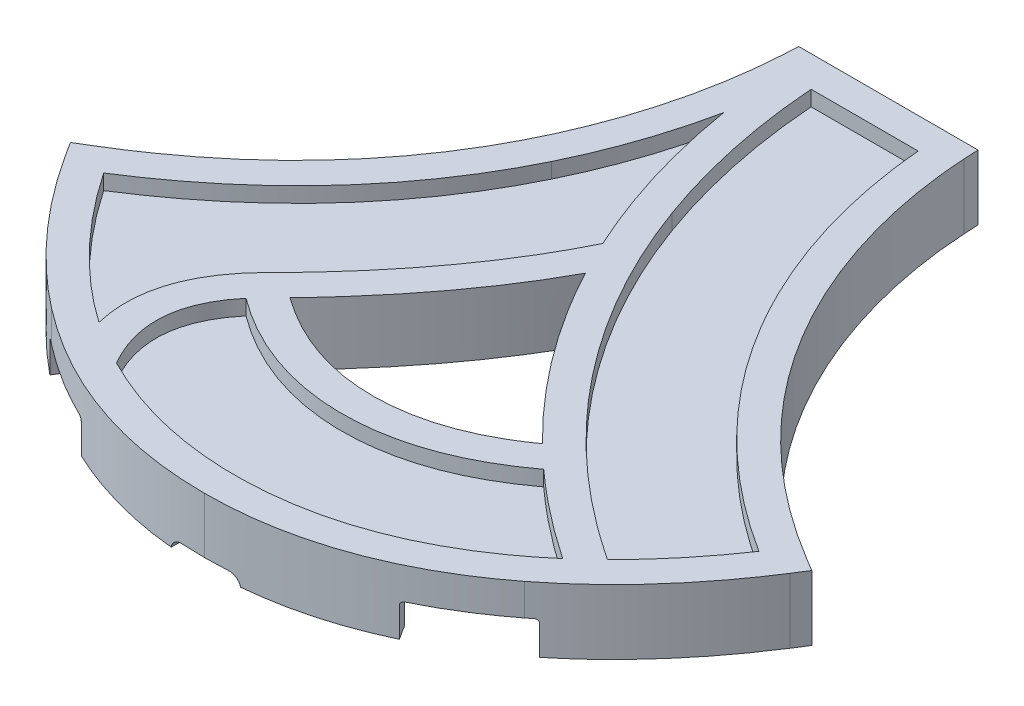
SolidWorks part; units mm, degrees
material "Default Heavy"
ref_plane "Front \"XY\"" through (0, 0, 0) normal (0, 0, 1) x (1, 0, 0)
ref_plane "Top \"XZ\"" through (0, 0, 0) normal (0, 1, 0) x (1, 0, 0)
ref_plane "Right \"YZ\"" through (0, 0, 0) normal (1, 0, 0) x (0, 0, -1)
sketch "Sketch1" plane through (0, 0, 0) normal (0, 1, 0) x (1, 0, 0)
  line L32 (11.7402, 44.8006) -> (-11.7315, 44.8006) construction
  line L33 (11.7402, 44.8006) -> (-11.7315, 44.8006) construction
  line L34 (-46.7664, -12.7009) -> (-48.5396, -13.7694) construction
  line L35 (-11.7315, 44.8006) -> (-11.8354, 42.8927) construction
  line L36 (47.433, -15.5188) -> (48.547, -13.7736) construction
  line L37 (-48.5396, -13.7694) -> (-47.426, -15.5143) construction
  line L38 (11.8441, 42.8927) -> (11.7402, 44.8006) construction
  line L39 (48.547, -13.7736) -> (46.7735, -12.7051) construction
  line L40 (11.7402, 44.8006) -> (-11.7315, 44.8006)
  line L41 (11.7402, 44.8006) -> (-11.7315, 44.8006)
  line L42 (-46.7664, -12.7009) -> (-48.5396, -13.7694)
  line L43 (-11.7315, 44.8006) -> (-11.8354, 42.8927)
  line L44 (47.433, -15.5188) -> (48.547, -13.7736)
  line L45 (-48.5396, -13.7694) -> (-47.426, -15.5143)
  line L46 (11.8441, 42.8927) -> (11.7402, 44.8006)
  line L47 (48.547, -13.7736) -> (46.7735, -12.7051)
  line L48 (11.7402, 44.8006) -> (-11.7315, 44.8006)
  spline S16 degree 3 poles (13707.5926, -20824.3124) (-15245.721, 20050.3834) (16897.5102, -18500.0295) (-18773.6133, 16415.021) knots -4.837537 -4.837537 -4.837537 -4.837537 13.412355 13.412355 13.412355 13.412355 only from (-11.8354, 42.8927) to (-46.7664, -12.7009) construction
  spline S17 degree 3 poles (1539.6845, -24946.8696) (-345.1015, 25306.6263) (-1470.73, -25271.221) (3595.9316, 24629.0284) knots -11.779696 -11.779696 -11.779696 -11.779696 27.004218 27.004218 27.004218 27.004218 only from (-47.426, -15.5143) to (-30.9593, -33.8177) construction
  spline S18 degree 3 poles (21323.4082, 11255.2499) (-19481.8243, 1044.4638) (16093.481, -12042.5003) (-11459.5819, 21515.9032) knots -31.449224 -31.449224 -31.449224 -31.449224 46.962215 46.962215 46.962215 46.962215 only from (-30.9593, -33.8177) to (0.0044, -44.7764) construction
  spline S19 degree 3 poles (11483.557, 21502.7967) (-16112.02, -12023.9333) (19492.4249, 1026.6895) (-21324.7799, 11264.6859) knots -28.966744 -28.966744 -28.966744 -28.966744 49.442095 49.442095 49.442095 49.442095 only from (0.0044, -44.7764) to (30.9639, -33.8206) construction
  spline S21 degree 3 poles (-3597.2153, 24627.9956) (1471.8367, -25270.9645) (344.2614, 25307.2023) (-1539.1086, -24948.3129) knots -9.003943 -9.003943 -9.003943 -9.003943 29.780059 29.780059 29.780059 29.780059 only from (30.9639, -33.8206) to (47.433, -15.5188) construction
  spline S23 degree 3 poles (18768.5213, 16420.8604) (-16891.8994, -18504.907) (15239.7814, 20054.0475) (-13701.4196, -20826.6216) knots -8.411838 -8.411838 -8.411838 -8.411838 9.836602 9.836602 9.836602 9.836602 only from (46.7735, -12.7051) to (11.8441, 42.8927) construction
  spline S27 degree 3 poles (-11.8354, 42.8927) (-12.42, 32.1531) (-16.9942, 5.2374) (-46.7664, -12.7009) knots 4 4 4 4 5 5 5 5
  spline S28 degree 3 poles (-47.426, -15.5143) (-44.2218, -20.5355) (-38.764, -27.7869) (-30.9593, -33.8177) knots 7 7 7 7 8 8 8 8
  spline S29 degree 3 poles (-30.9593, -33.8177) (-21.5489, -41.0893) (-11.1312, -44.7764) (0.0044, -44.7764) knots 8 8 8 8 9 9 9 9
  spline S30 degree 3 poles (0.0044, -44.7764) (11.1376, -44.7764) (21.554, -41.0903) (30.9639, -33.8206) knots 9 9 9 9 10 10 10 10
  spline S31 degree 3 poles (30.9639, -33.8206) (38.7697, -27.7903) (44.2283, -20.5394) (47.433, -15.5188) knots 10 10 10 10 11 11 11 11
  spline S32 degree 3 poles (46.7735, -12.7051) (17.0035, 5.2298) (12.4291, 32.1508) (11.8441, 42.8927) knots 0 0 0 0 1 1 1 1
  spline S33 degree 3 poles (-22689.4131, 7516.3472) (50.058, 6093.499) (323.9531, -22.7171) (0.0044, -22.7171) (-324.142, -22.7171) (-49.4306, 6101.5423) (22711.8041, 7432.6911) knots -55.485032 -55.485032 -55.485032 -55.485032 1 1 1 57.365232 57.365232 57.365232 57.365232 only from (16.5263, -17.0261) to (-16.5604, -16.995) construction
  spline S34 degree 3 poles (-11026.4564, -22396.6328) (12800.7603, 21635.8317) (-14894.9391, -20098.3724) (17282.0639, 17882.0255) knots -25.324219 -25.324219 -25.324219 -25.324219 30.628889 30.628889 30.628889 30.628889 only from (0, 5.1275) to (16.5263, -17.0261) construction
  spline S35 degree 3 poles (1892.6976, 23618.6805) (-11466.4056, -21362.8263) (17398.9855, 17827.8021) (-20670.1303, -13617.4284) knots -53.46671 -53.46671 -53.46671 -53.46671 51.151619 51.151619 51.151619 51.151619 only from (-16.5604, -16.995) to (0, 5.1275) construction
  spline S36 degree 3 poles (16.5263, -17.0261) (11.2873, -20.8001) (5.7395, -22.7171) (0.0044, -22.7171) (-5.7464, -22.7171) (-11.3088, -20.7894) (-16.5604, -16.995) knots 0 0 0 0 1 1 1 2 2 2 2
  spline S37 degree 3 poles (0, 5.1275) (3.7422, -1.9338) (9.039, -9.6332) (16.5263, -17.0261) knots 3 3 3 3 4 4 4 4
  spline S38 degree 3 poles (-16.5604, -16.995) (-9.5786, -9.7673) (-4.0267, -2.348) (0, 5.1275) knots 2 2 2 2 3 3 3 3
extrude "Boss-Extrude1" add sketch "Sketch1" along normal blind 2.5 contours L47 S32 L46 L40 L43 S27 L42 L45 S28 S29 S30 S31 L44 S36 S38 S37
sketch "Sketch4" plane through (0, 0, 0) normal (0, -1, 0) x (1, 0, 0)
  line L10 (11.8441, -42.8927) -> (11.7402, -44.8006) construction
  line L11 (48.547, 13.7736) -> (46.7735, 12.7051) construction
  line L12 (11.7402, -44.8006) -> (-11.7315, -44.8006) construction
  line L13 (-46.7664, 12.7009) -> (-48.5396, 13.7694) construction
  line L14 (-11.7315, -44.8006) -> (-11.8354, -42.8927) construction
  line L15 (47.433, 15.5188) -> (48.547, 13.7736) construction
  line L16 (-48.5396, 13.7694) -> (-47.426, 15.5143) construction
  line L17 (11.8441, -42.8927) -> (11.7402, -44.8006)
  line L18 (48.547, 13.7736) -> (46.7735, 12.7051)
  line L19 (11.7402, -44.8006) -> (-11.7315, -44.8006)
  line L20 (-46.7664, 12.7009) -> (-48.5396, 13.7694)
  line L21 (-11.7315, -44.8006) -> (-11.8354, -42.8927)
  line L22 (47.433, 15.5188) -> (48.547, 13.7736)
  line L23 (-48.5396, 13.7694) -> (-47.426, 15.5143)
  line L27 (7.0684, -42.5506) -> (-7.0596, -42.5506)
  line L31 (-45.4008, 14.5046) -> (-45.4008, 14.5046) construction
  line L32 (-45.4008, 14.5046) -> (-45.4008, 14.5046) construction
  line L33 (45.4079, 14.5088) -> (45.4079, 14.5088) construction
  line L34 (45.4079, 14.5088) -> (45.4079, 14.5088) construction
  line L35 (9.6098, -42.5506) -> (-9.6011, -42.5506) construction
  line L36 (-9.6011, -42.5506) -> (-9.6011, -42.5506) construction
  line L37 (9.6098, -42.5506) -> (9.6098, -42.5506) construction
  arc A8 (-43.7947, 16.9011) -> (-43.039, 13.0216) centre (-41.5398, 15.327) ccw
  arc A9 (43.8013, 16.9056) -> (43.0458, 13.0258) centre (41.5466, 15.3312) cw
  arc A10 (-9.7963, -40.0708) -> (-7.0596, -42.5506) centre (-7.0596, -39.8006) ccw
  arc A11 (7.0684, -42.5506) -> (9.8051, -40.0708) centre (7.0684, -39.8006) ccw
  arc A12 (-18.5794, 18.3121) -> (-18.7798, 16.0541) centre (-17.7009, 17.0963) ccw
  arc A13 (18.5615, 18.3331) -> (18.7386, 16.0486) centre (17.6847, 17.116) cw
  arc A14 (-1.3152, -7.4304) -> (1.3308, -7.4214) centre (0.0054, -6.719) ccw
  spline S0 degree 1 poles (-45.4008, 14.5046) (-29.5836, 32.0373) knots 0 0 1 1 construction
  spline S1 degree 1 poles (-29.5836, 32.0373) (0.0044, 42.5264) knots 0 0 1 1 construction
  spline S2 degree 1 poles (0.0044, 42.5264) (29.5883, 32.04) knots 0 0 1 1 construction
  spline S3 degree 1 poles (29.5883, 32.04) (45.4079, 14.5088) knots 0 0 1 1 construction
  spline S4 degree 1 poles (45.4079, 14.5088) (9.6098, -42.5506) knots 0 0 1 1 construction
  spline S5 degree 1 poles (-9.6011, -42.5506) (-45.4008, 14.5046) knots 0 0 1 1 construction
  spline S6 degree 3 poles (1803.2949, -917.1286) (-1413.7247, 1426.3175) (1143.7595, -1785.5106) (-885.202, 1742.7475) knots -3.201509 -3.201509 -3.201509 -3.201509 4.674641 4.674641 4.674641 4.674641 only from (46.7735, 12.7051) to (11.8441, -42.8927) construction
  spline S7 degree 3 poles (885.5961, 1742.5426) (-1144.1453, -1785.128) (1414.1117, 1425.791) (-1803.61, -916.5575) knots 0.325017 0.325017 0.325017 0.325017 8.201625 8.201625 8.201625 8.201625 only from (-11.8354, -42.8927) to (-46.7664, 12.7009) construction
  spline S8 degree 3 poles (-656.5291, -1830.5216) (211.0906, 2136.1853) (197.0374, -2121.6865) (-250.135, 1992.3469) knots 1.9887 1.9887 1.9887 1.9887 18.868565 18.868565 18.868565 18.868565 only from (30.9639, 33.8206) to (47.433, 15.5188) construction
  spline S9 degree 3 poles (-182.7302, -1916.5345) (-625.9753, 964.0535) (972.7294, 379.8096) (-706.3522, -1787.4548) knots -3.602256 -3.602256 -3.602256 -3.602256 22.781955 22.781955 22.781955 22.781955 only from (0.0044, 44.7764) to (30.9639, 33.8206) construction
  spline S10 degree 3 poles (706.2836, -1787.507) (-972.1545, 379.053) (624.8527, 964.7445) (184.0184, -1916.4925) knots -4.782528 -4.782528 -4.782528 -4.782528 21.598996 21.598996 21.598996 21.598996 only from (-30.9593, 33.8177) to (0.0044, 44.7764) construction
  spline S11 degree 3 poles (250.1669, 1992.3048) (-197.0811, -2121.6951) (-210.9874, 2136.2153) (656.3732, -1830.5639) knots -0.86853 -0.86853 -0.86853 -0.86853 16.011373 16.011373 16.011373 16.011373 only from (-47.426, 15.5143) to (-30.9593, 33.8177) construction
  spline S12 degree 3 poles (46.7735, 12.7051) (17.0035, -5.2298) (12.4291, -32.1508) (11.8441, -42.8927) knots 0 0 0 0 1 1 1 1
  spline S13 degree 3 poles (-11.8354, -42.8927) (-12.42, -32.1531) (-16.9942, -5.2374) (-46.7664, 12.7009) knots 4 4 4 4 5 5 5 5
  spline S14 degree 1 poles (20.0016, 17.2956) (-19.982, 17.2987) knots 0 0 1 1 construction
  spline S15 degree 1 poles (-19.982, 17.2987) (0.0161, -9.902) knots 0 0 1 1 construction
  spline S16 degree 1 poles (0.0161, -9.902) (20.0016, 17.2956) knots 0 0 1 1 construction
  spline S17 degree 3 poles (-656.972, 1882.3837) (895.1742, -1896.2916) (-1266.5252, 1551.0515) (1736.0801, -964.3246) knots -9.517328 -9.517328 -9.517328 -9.517328 14.561888 14.561888 14.561888 14.561888 only from (0, -5.1275) to (16.5263, 17.0261) construction
  spline S18 degree 3 poles (-812.1216, -1756.1775) (153.3939, -723.9366) (113.1908, 22.7171) (0.0044, 22.7171) (-113.2755, 22.7171) (-153.4167, -725.2403) (813.7688, -1755.1904) knots -18.735656 -18.735656 -18.735656 -18.735656 1 1 1 20.698036 20.698036 20.698036 20.698036 only from (16.5263, 17.0261) to (-16.5604, 16.995) construction
  spline S19 degree 3 poles (-1494.9401, -1107.0542) (-493.0371, 1462.3088) (1527.6763, -1118.2051) (-1935.6902, 373.726) knots -19.400052 -19.400052 -19.400052 -19.400052 21.459168 21.459168 21.459168 21.459168 only from (-16.5604, 16.995) to (0, -5.1275) construction
  spline S20 degree 3 poles (30.9639, 33.8206) (38.7697, 27.7903) (44.2283, 20.5394) (47.433, 15.5188) knots 10 10 10 10 11 11 11 11
  spline S21 degree 3 poles (0.0044, 44.7764) (11.1376, 44.7764) (21.554, 41.0903) (30.9639, 33.8206) knots 9 9 9 9 10 10 10 10
  spline S22 degree 3 poles (-30.9593, 33.8177) (-21.5489, 41.0893) (-11.1312, 44.7764) (0.0044, 44.7764) knots 8 8 8 8 9 9 9 9
  spline S23 degree 3 poles (-47.426, 15.5143) (-44.2218, 20.5355) (-38.764, 27.7869) (-30.9593, 33.8177) knots 7 7 7 7 8 8 8 8
  spline S24 degree 3 poles (-45.4008, 14.5046) (-45.1993, 14.818) (-44.8052, 15.4216) (-44.3123, 16.1525) (-43.9137, 16.7311) (-43.4344, 17.4177) (-42.4848, 18.7375) (-41.0114, 20.6683) (-38.5096, 23.7002) (-35.6003, 26.8157) (-32.3026, 29.8474) (-30.4978, 31.3308) (-29.5836, 32.0373) knots 7.013641 7.013641 7.013641 7.013641 7.075288 7.135505 7.150917 7.181741 7.260231 7.383525 7.50682 7.75341 7.876705 8 8 8 8 only from (-43.7947, 16.9011) to (-29.5836, 32.0373)
  spline S25 degree 3 poles (-29.5836, 32.0373) (-29.0215, 32.4716) (-27.875, 33.3247) (-25.5723, 34.9076) (-22.6403, 36.6839) (-19.0496, 38.4843) (-14.1648, 40.4483) (-9.1321, 41.7588) (-3.9659, 42.4164) (-1.3145, 42.5264) (0.0044, 42.5264) knots 8 8 8 8 8.0625 8.125 8.25 8.375 8.5 8.75 8.875 9 9 9 9
  spline S26 degree 3 poles (0.0044, 42.5264) (1.323, 42.5264) (3.9739, 42.4164) (9.1391, 41.759) (14.171, 40.4488) (19.0553, 38.4854) (22.6455, 36.6855) (25.5773, 34.9097) (27.8799, 33.3271) (29.0263, 32.4742) (29.5883, 32.04) knots 9 9 9 9 9.125 9.25 9.5 9.625 9.75 9.875 9.9375 10 10 10 10
  spline S27 degree 3 poles (29.5883, 32.04) (30.5027, 31.3336) (32.3078, 29.8503) (35.6059, 26.8189) (38.5156, 23.7036) (41.0179, 20.672) (42.4913, 18.7415) (43.441, 17.422) (43.9203, 16.7355) (44.3191, 16.1569) (44.8122, 15.4259) (45.2064, 14.8222) (45.4079, 14.5088) knots 9.999999 9.999999 9.999999 9.999999 10.123294 10.246588 10.493177 10.616472 10.739766 10.81823 10.849054 10.864466 10.924708 10.986355 10.986355 10.986355 10.986355 only from (29.5883, 32.04) to (43.8013, 16.9056)
  spline S28 degree 3 poles (45.4079, 14.5088) (44.8128, 14.1482) (43.8135, 13.5262) (42.0129, 12.3551) (39.0954, 10.3496) (35.1379, 7.2909) (30.8576, 3.4304) (25.8129, -1.8595) (20.6827, -8.6402) (16.1679, -16.7402) (13.048, -24.4997) (11.4011, -30.4358) (10.5296, -34.7203) (10.098, -37.4733) (9.8808, -39.3004) (9.7577, -40.5487) (9.6768, -41.5052) (9.6313, -42.1823) (9.6098, -42.5506) knots 0.002236 0.002236 0.002236 0.002236 0.022081 0.035311 0.064191 0.126145 0.1881 0.250054 0.373963 0.497872 0.621781 0.74569 0.807644 0.869598 0.919268 0.934756 0.96253 0.993507 0.993507 0.993507 0.993507 only from (43.0458, 13.0258) to (9.8051, -40.0708)
  spline S29 degree 3 poles (-9.6011, -42.5506) (-9.6225, -42.1824) (-9.668, -41.5053) (-9.7489, -40.5488) (-9.872, -39.3007) (-10.0891, -37.4741) (-10.5207, -34.7218) (-11.3922, -30.438) (-13.0391, -24.5029) (-16.1591, -16.7443) (-20.6741, -8.6451) (-25.8046, -1.8647) (-30.8496, 3.4252) (-35.1301, 7.2858) (-39.0881, 10.3449) (-42.0059, 12.3507) (-43.8066, 13.522) (-44.8058, 14.1439) (-45.4008, 14.5046) knots 4.006495 4.006495 4.006495 4.006495 4.037472 4.065257 4.080746 4.130403 4.192358 4.254312 4.378221 4.502129 4.626038 4.749947 4.811901 4.873855 4.93581 4.964697 4.977924 4.997764 4.997764 4.997764 4.997764 only from (-9.7963, -40.0708) to (-43.039, 13.0216)
  spline S30 degree 3 poles (0, -5.1275) (3.7422, 1.9338) (9.039, 9.6332) (16.5263, 17.0261) knots 3 3 3 3 4 4 4 4
  spline S31 degree 3 poles (16.5263, 17.0261) (11.2873, 20.8001) (5.7395, 22.7171) (0.0044, 22.7171) (-5.7464, 22.7171) (-11.3088, 20.7894) (-16.5604, 16.995) knots 0 0 0 0 1 1 1 2 2 2 2
  spline S32 degree 3 poles (-16.5604, 16.995) (-9.5786, 9.7673) (-4.0267, 2.348) (0, -5.1275) knots 2 2 2 2 3 3 3 3
  spline S33 degree 3 poles (20.0016, 17.2956) (19.6138, 17.575) (19.0409, 17.9876) (18.2984, 18.5226) (17.5637, 19.0513) (16.5747, 19.7393) (14.9744, 20.7501) (12.9322, 21.8797) (9.603, 23.366) (5.3275, 24.6235) (0.0454, 25.1357) (-5.2638, 24.6357) (-9.5496, 23.3824) (-12.8892, 21.8968) (-14.9374, 20.7667) (-16.5425, 19.7545) (-17.5489, 19.0561) (-18.3022, 18.5124) (-19.0462, 17.9748) (-19.6063, 17.5701) (-19.982, 17.2987) knots -0.137443 -0.137443 -0.137443 -0.137443 -0.063557 -0.028072 0.004493 0.075461 0.14643 0.288366 0.430303 0.714176 0.998049 1.281922 1.565795 1.707732 1.849668 1.920636 1.991605 2.026772 2.062256 2.133541 2.133541 2.133541 2.133541 only from (18.5615, 18.3331) to (-18.5794, 18.3121)
  spline S34 degree 3 poles (-19.982, 17.2987) (-19.6814, 16.9876) (-19.1812, 16.4694) (-18.5789, 15.8463) (-17.7934, 15.0311) (-16.1628, 13.3221) (-13.6979, 10.5792) (-10.8922, 7.2085) (-7.4378, 2.6925) (-4.7989, -1.2759) (-2.8048, -4.685) (-2.0802, -6.0114) (-1.5014, -7.0846) (-0.8713, -8.2547) (-0.3489, -9.2243) (0.0161, -9.902) knots 1.913903 1.913903 1.913903 1.913903 1.956951 1.98565 2 2.070329 2.226756 2.383183 2.539609 2.852463 2.930676 3.00889 3.035552 3.074659 3.165316 3.165316 3.165316 3.165316 only from (-18.7798, 16.0541) to (-1.3152, -7.4304)
  spline S35 degree 3 poles (0.0161, -9.902) (0.3448, -9.2819) (0.8926, -8.2494) (1.5498, -7.0071) (2.4005, -5.4132) (4.2333, -2.0674) (7.0594, 2.3493) (10.4823, 6.9426) (13.335, 10.3966) (15.9235, 13.233) (17.6722, 14.9929) (18.5275, 15.8403) (19.1605, 16.4648) (19.6859, 16.9839) (20.0016, 17.2956) knots 2.824352 2.824352 2.824352 2.824352 2.912176 2.970725 3 3.139349 3.454347 3.611845 3.769344 3.926842 4 4.014057 4.042171 4.084341 4.084341 4.084341 4.084341 only from (1.3308, -7.4214) to (18.7386, 16.0486)
  dimension "D3" = 2.25
  dimension "D2" = 2.75
  dimension "D4" = 1.5
  dimension "D1" = 2.25
extrude "Boss-Extrude4" add sketch "Sketch4" along normal blind 4
sketch "Sketch15" plane through (0, 0, 0) normal (0, -1, 0) x (1, 0, 0)
  arc A12 (39.5784, 17.9174) -> (38.8845, 13.4669) centre (41.5466, 15.3312) ccw
  arc A13 (43.0458, 13.0258) -> (43.8013, 16.9056) centre (41.5466, 15.3312) ccw construction
  arc A14 (38.2872, 9.6934) -> (38.8845, 13.4669) centre (36.6319, 11.8894) ccw
  arc A15 (39.5784, 17.9174) -> (40.0305, 21.8605) centre (37.913, 20.1058) ccw
  arc A16 (43.0458, 13.0258) -> (43.8013, 16.9056) centre (41.5466, 15.3312) ccw construction
  arc A17 (43.0458, 13.0258) -> (43.8013, 16.9056) centre (41.5466, 15.3312) ccw
  arc A18 (-39.5719, 17.9135) -> (-38.8777, 13.4627) centre (-41.5398, 15.327) cw
  arc A19 (-38.8777, 13.4627) -> (-38.2805, 9.6891) centre (-36.6252, 11.8851) ccw
  arc A20 (-39.5719, 17.9135) -> (-40.0245, 21.8565) centre (-37.9068, 20.1021) cw
  arc A21 (-43.7947, 16.9011) -> (-43.039, 13.0216) centre (-41.5398, 15.327) ccw construction
  arc A22 (-43.7947, 16.9011) -> (-43.039, 13.0216) centre (-41.5398, 15.327) ccw
  arc A23 (-2.7443, -9.6779) -> (2.7511, -9.6688) centre (0.0054, -10.8775) ccw
  arc A26 (-1.3152, -7.4304) -> (1.3308, -7.4214) centre (0.0054, -6.719) ccw construction
  arc A32 (2.2258, -8.8602) -> (-2.218, -8.8634) centre (0.0054, -10.8775) ccw construction
  arc A33 (2.7511, -9.6688) -> (3.0034, -4.3271) centre (8.2425, -7.2513) cw
  arc A34 (-2.7443, -9.6779) -> (-3.0409, -4.2901) centre (-8.2437, -7.2786) ccw
  arc A35 (-1.3152, -7.4304) -> (1.3308, -7.4214) centre (0.0054, -6.719) ccw
  spline S0 degree 3 poles (-169.4967, 1984.8018) (-38.3645, -103.1789) (-18.7497, -45.0426) (2.4005, -5.4132) (4.2333, -2.0674) (7.0594, 2.3493) (10.4823, 6.9426) (13.335, 10.3966) (15.9235, 13.233) (17.6722, 14.9929) (38.4208, 35.5517) (74.4226, 65.524) (-1682.994, -1034.3687) knots -2.50892 -2.50892 -2.50892 -2.50892 2.970725 3 3.139349 3.454347 3.611845 3.769344 3.926842 4 4.014057 6.724831 6.724831 6.724831 6.724831 only from (1.3308, -7.4214) to (18.7386, 16.0486) construction
  spline S1 degree 3 poles (1631.8648, -1113.2073) (-74.0621, 68.5967) (-39.0819, 37.1261) (-17.7934, 15.0311) (-16.1628, 13.3221) (-13.6979, 10.5792) (-10.8922, 7.2085) (-7.4378, 2.6925) (-4.7989, -1.2759) (-2.8048, -4.685) (-2.0802, -6.0114) (20.9082, -48.6334) (47.4001, -103.4293) (-547.1028, 1916.5502) knots -1.002674 -1.002674 -1.002674 -1.002674 1.98565 2 2.070329 2.226756 2.383183 2.539609 2.852463 2.930676 3.00889 3.035552 8.648932 8.648932 8.648932 8.648932 only from (-18.7798, 16.0541) to (-1.3152, -7.4304) construction
  spline S2 degree 3 poles (436.8081, -1989.4341) (-43.8071, -10.4264) (-5.3621, -77.2452) (-10.0891, -37.4741) (-10.5207, -34.7218) (-11.3922, -30.438) (-13.0391, -24.5029) (-16.1591, -16.7443) (-20.6741, -8.6451) (-25.8046, -1.8647) (-30.8496, 3.4252) (-35.1301, 7.2858) (-39.0881, 10.3449) (-76.8288, 36.2892) (-153.0863, 46.6033) (-1827.7211, 915.2579) knots 1.424907 1.424907 1.424907 1.424907 4.080746 4.130403 4.192358 4.254312 4.378221 4.502129 4.626038 4.749947 4.811901 4.873855 4.93581 4.964697 6.219948 6.219948 6.219948 6.219948 only from (-9.7963, -40.0708) to (-43.039, 13.0216) construction
  spline S3 degree 3 poles (-1974.2948, -505.5877) (80.6735, 51.2005) (-82.1251, -36.3531) (-42.4848, 18.7375) (-41.0114, 20.6683) (-38.5096, 23.7002) (-35.6003, 26.8157) (-1.2592, 58.3869) (92.7423, 75.704) (-1326.3464, -1489.6908) knots -2.326031 -2.326031 -2.326031 -2.326031 7.181741 7.260231 7.383525 7.50682 7.75341 7.876705 12.642642 12.642642 12.642642 12.642642 only from (-43.7947, 16.9011) to (-29.5836, 32.0373) construction
  spline S4 degree 3 poles (1827.9044, 915.0837) (153.1259, 46.5938) (76.8432, 36.2974) (39.0954, 10.3496) (35.1379, 7.2909) (30.8576, 3.4304) (25.8129, -1.8595) (20.6827, -8.6402) (16.1679, -16.7402) (13.048, -24.4997) (11.4011, -30.4358) (10.5296, -34.7203) (10.098, -37.4733) (5.3703, -77.2547) (43.8176, -10.4113) (-436.8926, -1989.4182) knots -1.220292 -1.220292 -1.220292 -1.220292 0.035311 0.064191 0.126145 0.1881 0.250054 0.373963 0.497872 0.621781 0.74569 0.807644 0.869598 0.919268 3.575324 3.575324 3.575324 3.575324 only from (43.0458, 13.0258) to (9.8051, -40.0708) construction
  spline S5 degree 3 poles (1326.6537, -1489.4071) (-92.7323, 75.7001) (1.2649, 58.3827) (35.6059, 26.8189) (38.5156, 23.7036) (41.0179, 20.672) (42.4913, 18.7415) (82.22, -36.4579) (-81.3528, 51.5617) (1977.6406, -493.0666) knots 5.358134 5.358134 5.358134 5.358134 10.123294 10.246588 10.493177 10.616472 10.739766 10.81823 20.345994 20.345994 20.345994 20.345994 only from (29.5883, 32.04) to (43.8013, 16.9056) construction
  spline S6 degree 3 poles (43.0458, 13.0258) (42.8533, 12.9006) (41.8274, 12.2276) (40.2214, 11.1236) (38.8611, 10.126) (38.2872, 9.6934) knots 0.028696 0.028696 0.028696 0.028696 0.035311 0.064191 0.085982 0.085982 0.085982 0.085982
  spline S7 degree 3 poles (40.0305, 21.8605) (40.3576, 21.4657) (41.2852, 20.3217) (42.4913, 18.7415) (43.3781, 17.5094) (43.7421, 16.9904) (43.8013, 16.9056) knots 10.552157 10.552157 10.552157 10.552157 10.616472 10.739766 10.81823 10.833642 10.833642 10.833642 10.833642
  spline S8 degree 3 poles (-38.2805, 9.6891) (-38.8541, 10.1215) (-40.2145, 11.1192) (-41.8205, 12.2233) (-42.8466, 12.8965) (-43.039, 13.0216) knots 4.914029 4.914029 4.914029 4.914029 4.93581 4.964697 4.971311 4.971311 4.971311 4.971311
  spline S9 degree 3 poles (-43.7947, 16.9011) (-43.7355, 16.986) (-43.3715, 17.5051) (-42.4848, 18.7375) (-41.2788, 20.3179) (-40.3515, 21.4618) (-40.0245, 21.8565) knots 7.166329 7.166329 7.166329 7.166329 7.181741 7.260231 7.383525 7.44782 7.44782 7.44782 7.44782
  spline S12 degree 3 poles (1.3308, -7.4214) (1.4403, -7.2147) (1.6594, -6.8017) (2.2115, -5.7672) (2.6578, -4.9463) (3.0034, -4.3271) knots 2.941451 2.941451 2.941451 2.941451 2.970725 3 3.088891 3.088891 3.088891 3.088891
  spline S13 degree 3 poles (-3.0409, -4.2901) (-2.9654, -4.4215) (-2.5669, -5.1205) (-2.0802, -6.0114) (-1.58, -6.9389) (-1.394, -7.2842) (-1.3152, -7.4304) knots 2.912572 2.912572 2.912572 2.912572 2.930676 3.00889 3.035552 3.055105 3.055105 3.055105 3.055105
  dimension "D1" = 2.75
  dimension "D2" = 3
  dimension "D3" = 6
  dimension "D4" = 5.75
  dimension "D5" = 3.25
extrude "Boss-Extrude6" add sketch "Sketch15" along normal up to surface (4 mm away) up to face at (0.9652, -4, 1.6162)
sketch "Sketch23" plane through (0, -4, 0) normal (0, -1, 0) x (1, 0, 0)
  circle A0 centre (-41.5398, 15.327) radius 1.675
  circle A1 centre (0.0054, -10.8775) radius 1.675
  circle A2 centre (41.5466, 15.3312) radius 1.675
  dimension "D1" = 3.35
extrude "Cut-Extrude5" cut sketch "Sketch23" against normal blind 4.5
sketch "Sketch12" plane through (0, 2.5, 0) normal (0, 1, 0) x (1, 0, 0)
  line L7 (-6.0753, 40.7654) -> (7.9467, 40.7654)
  line L8 (-46.7664, -12.7009) -> (-48.5396, -13.7694) construction
  line L9 (-11.7315, 44.8006) -> (-11.8354, 42.8927) construction
  line L10 (47.433, -15.5188) -> (48.547, -13.7736) construction
  line L11 (-48.5396, -13.7694) -> (-47.426, -15.5143) construction
  line L12 (11.8441, 42.8927) -> (11.7402, 44.8006) construction
  line L13 (48.547, -13.7736) -> (46.7735, -12.7051) construction
  line L14 (11.7402, 44.8006) -> (-11.7315, 44.8006) construction
  line L15 (-46.7664, -12.7009) -> (-48.5396, -13.7694)
  line L16 (-11.7315, 44.8006) -> (-11.8354, 42.8927)
  line L17 (47.433, -15.5188) -> (48.547, -13.7736)
  line L18 (-48.5396, -13.7694) -> (-47.426, -15.5143)
  line L19 (11.8441, 42.8927) -> (11.7402, 44.8006)
  line L20 (48.547, -13.7736) -> (46.7735, -12.7051)
  line L21 (11.7402, 44.8006) -> (-11.7315, 44.8006)
  spline S0 degree 3 poles (885.5961, -1742.5426) (-1144.1453, 1785.128) (1414.1117, -1425.791) (-1803.61, 916.5575) knots 0.325017 0.325017 0.325017 0.325017 8.201625 8.201625 8.201625 8.201625 only from (-11.8354, 42.8927) to (-46.7664, -12.7009) construction
  spline S1 degree 3 poles (250.1669, -1992.3048) (-197.0811, 2121.6951) (-210.9874, -2136.2153) (656.3732, 1830.5639) knots -0.86853 -0.86853 -0.86853 -0.86853 16.011373 16.011373 16.011373 16.011373 only from (-47.426, -15.5143) to (-30.9593, -33.8177) construction
  spline S2 degree 3 poles (706.2836, 1787.507) (-972.1545, -379.053) (624.8527, -964.7445) (184.0184, 1916.4925) knots -4.782528 -4.782528 -4.782528 -4.782528 21.598996 21.598996 21.598996 21.598996 only from (-30.9593, -33.8177) to (0.0044, -44.7764) construction
  spline S3 degree 3 poles (-182.7302, 1916.5345) (-625.9753, -964.0535) (972.7294, -379.8096) (-706.3522, 1787.4548) knots -3.602256 -3.602256 -3.602256 -3.602256 22.781955 22.781955 22.781955 22.781955 only from (0.0044, -44.7764) to (30.9639, -33.8206) construction
  spline S4 degree 3 poles (-656.5291, 1830.5216) (211.0906, -2136.1853) (197.0374, 2121.6865) (-250.135, -1992.3469) knots 1.9887 1.9887 1.9887 1.9887 18.868565 18.868565 18.868565 18.868565 only from (30.9639, -33.8206) to (47.433, -15.5188) construction
  spline S5 degree 3 poles (1803.2949, 917.1286) (-1413.7247, -1426.3175) (1143.7595, 1785.5106) (-885.202, -1742.7475) knots -3.201509 -3.201509 -3.201509 -3.201509 4.674641 4.674641 4.674641 4.674641 only from (46.7735, -12.7051) to (11.8441, 42.8927) construction
  spline S6 degree 3 poles (-26.2671, -32.3028) (-33.7735, -27.0883) (-39.286, -20.3963) (-42.8998, -15.0545) knots 6 6 6 6 7 7 7 7
  spline S7 degree 3 poles (-21.0273, -15.7838) (-25.95, -20.7066) (-27.72, -26.4181) (-26.2671, -32.3028) knots 5 5 5 5 6 6 6 6
  spline S8 degree 3 poles (-2.2272, 9.6323) (-6.4059, 1.0674) (-12.7224, -7.479) (-21.0273, -15.7838) knots 4 4 4 4 5 5 5 5
  spline S9 degree 3 poles (-4.959, 16.2851) (-4.2007, 14.1949) (-3.2985, 11.964) (-2.2272, 9.6323) knots 3 3 3 3 4 4 4 4
  spline S10 degree 3 poles (-9.1537, 32.3968) (-8.3696, 27.6088) (-7.0743, 22.1155) (-4.959, 16.2851) knots 2 2 2 2 3 3 3 3
  spline S11 degree 3 poles (-14.8927, 15.5512) (-11.9606, 21.5683) (-10.1982, 27.3441) (-9.1537, 32.3968) knots 1 1 1 1 2 2 2 2
  spline S12 degree 3 poles (-42.8998, -15.0545) (-30.3262, -7.0839) (-20.909, 3.2047) (-14.8927, 15.5512) knots 0 0 0 0 1 1 1 1
  spline S13 degree 3 poles (0, 5.1275) (3.7422, -1.9338) (9.039, -9.6332) (16.5263, -17.0261) knots 3 3 3 3 4 4 4 4
  spline S14 degree 3 poles (-16.5604, -16.995) (-9.5786, -9.7673) (-4.0267, -2.348) (0, 5.1275) knots 2 2 2 2 3 3 3 3
  spline S15 degree 3 poles (16.5263, -17.0261) (11.2873, -20.8001) (5.7395, -22.7171) (0.0044, -22.7171) (-5.7464, -22.7171) (-11.3088, -20.7894) (-16.5604, -16.995) knots 0 0 0 0 1 1 1 2 2 2 2
  spline S16 degree 3 poles (30.8834, -28.7277) (23.2458, -35.3048) (13.0017, -40.7412) (0.0044, -40.7412) (-7.8162, -40.7412) (-14.6395, -38.7726) (-20.4984, -35.772) knots 4 4 4 4 5 5 5 6 6 6 6
  spline S17 degree 3 poles (19.51, -19.8465) (22.8871, -22.9053) (26.6618, -25.889) (30.8834, -28.7277) knots 3 3 3 3 4 4 4 4
  spline S18 degree 3 poles (-19.372, -19.9427) (-13.2945, -24.4615) (-6.7848, -26.7523) (0.0044, -26.7523) (6.8416, -26.7523) (13.3956, -24.4294) (19.51, -19.8465) knots 1 1 1 1 2 2 2 3 3 3 3
  spline S19 degree 3 poles (-20.4984, -35.772) (-23.8177, -30.0844) (-23.4372, -24.7686) (-19.372, -19.9427) knots 0 0 0 0 1 1 1 1
  spline S20 degree 3 poles (33.9362, -25.911) (13.0256, -12.1351) (3.31, 5.3244) (-1.1657, 17.6612) knots 0 0 0 0 1 1 1 1
  spline S21 degree 3 poles (-1.1657, 17.6612) (-4.4547, 26.727) (-5.6698, 34.9357) (-6.0753, 40.7654) knots 1 1 1 1 2 2 2 2
  spline S22 degree 3 poles (7.9467, 40.7654) (8.4835, 34.338) (10.1709, 25.255) (14.8992, 15.5491) knots 3 3 3 3 4 4 4 4
  spline S23 degree 3 poles (14.8992, 15.5491) (20.9146, 3.201) (30.3319, -7.0881) (42.9069, -15.0587) knots 4 4 4 4 5 5 5 5
  spline S24 degree 3 poles (42.9069, -15.0587) (40.659, -18.3807) (37.6756, -22.2247) (33.9362, -25.911) knots 5 5 5 5 6 6 6 6
  spline S25 degree 3 poles (-11.8354, 42.8927) (-12.42, 32.1531) (-16.9942, 5.2374) (-46.7664, -12.7009) knots 4 4 4 4 5 5 5 5
  spline S26 degree 3 poles (-47.426, -15.5143) (-44.2218, -20.5355) (-38.764, -27.7869) (-30.9593, -33.8177) knots 7 7 7 7 8 8 8 8
  spline S27 degree 3 poles (-30.9593, -33.8177) (-21.5489, -41.0893) (-11.1312, -44.7764) (0.0044, -44.7764) knots 8 8 8 8 9 9 9 9
  spline S28 degree 3 poles (0.0044, -44.7764) (11.1376, -44.7764) (21.554, -41.0903) (30.9639, -33.8206) knots 9 9 9 9 10 10 10 10
  spline S29 degree 3 poles (30.9639, -33.8206) (38.7697, -27.7903) (44.2283, -20.5394) (47.433, -15.5188) knots 10 10 10 10 11 11 11 11
  spline S30 degree 3 poles (46.7735, -12.7051) (17.0035, 5.2298) (12.4291, 32.1508) (11.8441, 42.8927) knots 0 0 0 0 1 1 1 1
extrude "Boss-Extrude5" add sketch "Sketch12" along normal blind 2
ref_plane "Plane1" through (-26.6231, -4, 36.8696) normal (-0.5373, 0, 0.8434) x (0.8434, 0, 0.5373)
sketch "Sketch20" plane through (0, 0, 0) normal (0, -1, 0) x (1, 0, 0)
  line L0 (-38.2805, 9.6891) -> (-18.7798, 16.0541)
  line L1 (-40.0245, 21.8565) -> (-18.5794, 18.3121)
  line L2 (38.2872, 9.6934) -> (18.7386, 16.0486)
  line L3 (40.0305, 21.8605) -> (18.5615, 18.3331)
  arc A0 (39.5784, 17.9174) -> (40.0305, 21.8605) centre (37.913, 20.1058) ccw construction
  arc A1 (39.5784, 17.9174) -> (38.8845, 13.4669) centre (41.5466, 15.3312) ccw construction
  arc A2 (38.2872, 9.6934) -> (38.8845, 13.4669) centre (36.6319, 11.8894) ccw construction
  arc A3 (18.7386, 16.0486) -> (18.5615, 18.3331) centre (17.6847, 17.116) ccw construction
  arc A4 (-18.5794, 18.3121) -> (-18.7798, 16.0541) centre (-17.7009, 17.0963) ccw construction
  arc A5 (-40.0245, 21.8565) -> (-39.5719, 17.9135) centre (-37.9068, 20.1021) ccw construction
  arc A6 (-38.8777, 13.4627) -> (-39.5719, 17.9135) centre (-41.5398, 15.327) ccw construction
  arc A7 (-38.8777, 13.4627) -> (-38.2805, 9.6891) centre (-36.6252, 11.8851) ccw construction
  arc A8 (39.5784, 17.9174) -> (40.0305, 21.8605) centre (37.913, 20.1058) ccw
  arc A9 (39.5784, 17.9174) -> (38.8845, 13.4669) centre (41.5466, 15.3312) ccw
  arc A10 (38.2872, 9.6934) -> (38.8845, 13.4669) centre (36.6319, 11.8894) ccw
  arc A11 (18.7386, 16.0486) -> (18.5615, 18.3331) centre (17.6847, 17.116) ccw
  arc A12 (-18.5794, 18.3121) -> (-18.7798, 16.0541) centre (-17.7009, 17.0963) ccw
  arc A13 (-40.0245, 21.8565) -> (-39.5719, 17.9135) centre (-37.9068, 20.1021) ccw
  arc A14 (-38.8777, 13.4627) -> (-39.5719, 17.9135) centre (-41.5398, 15.327) ccw
  arc A15 (-38.8777, 13.4627) -> (-38.2805, 9.6891) centre (-36.6252, 11.8851) ccw
extrude "Boss-Extrude7" add sketch "Sketch20" along normal up to surface (4 mm away) up to face at (0.0054, -4, -12.5525)
sketch "Sketch16" plane through (-26.6231, -4, 36.8696) normal (-0.5373, 0, 0.8434) x (0.8434, 0, 0.5373)
  line L4 (-6.1419, -1.85) -> (6.1581, -1.85)
  line L5 (6.6581, -1.35) -> (6.6581, 3.85)
  line L6 (6.1581, 4.35) -> (-6.1419, 4.35)
  line L7 (-6.6419, 3.85) -> (-6.6419, -1.35)
  line L8 (-6.1419, -1.85) -> (6.1581, -1.85)
  line L9 (6.6581, -1.35) -> (6.6581, 3.85)
  line L10 (6.1581, 4.35) -> (-6.1419, 4.35)
  line L11 (-6.6419, 3.85) -> (-6.6419, -1.35)
  arc A28 (6.1581, -1.85) -> (6.6581, -1.35) centre (6.1581, -1.35) ccw
  arc A29 (6.1581, -1.85) -> (6.6581, -1.35) centre (6.1581, -1.35) ccw
  arc A30 (6.6581, 3.85) -> (6.1581, 4.35) centre (6.1581, 3.85) ccw
  arc A31 (6.6581, 3.85) -> (6.1581, 4.35) centre (6.1581, 3.85) ccw
  arc A32 (-6.1419, 4.35) -> (-6.6419, 3.85) centre (-6.1419, 3.85) ccw
  arc A33 (-6.1419, 4.35) -> (-6.6419, 3.85) centre (-6.1419, 3.85) ccw
  arc A34 (-6.6419, -1.35) -> (-6.1419, -1.85) centre (-6.1419, -1.35) ccw
  arc A35 (-6.6419, -1.35) -> (-6.1419, -1.85) centre (-6.1419, -1.35) ccw
  dimension "D1" = 0
extrude "Cut-Extrude1" cut sketch "Sketch16" against normal blind 15
ref_plane "Plane2" through (0.0044, -4, 44.7764) normal (0, 0, 1) x (1, 0, 0)
sketch "Sketch17" plane through (0.0044, -4, 44.7764) normal (0, 0, 1) x (1, 0, 0)
  line L4 (-3.0774, -2.645) -> (3.0626, -2.645)
  line L5 (-4.5774, -0.295) -> (-4.5774, -1.145)
  line L6 (3.0626, 1.205) -> (-3.0774, 1.205)
  line L7 (4.5626, -1.145) -> (4.5626, -0.295)
  line L8 (-3.0774, -2.645) -> (3.0626, -2.645)
  line L9 (-4.5774, -0.295) -> (-4.5774, -1.145)
  line L10 (3.0626, 1.205) -> (-3.0774, 1.205)
  line L11 (4.5626, -1.145) -> (4.5626, -0.295)
  arc A28 (-4.5774, -1.145) -> (-3.0774, -2.645) centre (-3.0774, -1.145) ccw
  arc A29 (-4.5774, -1.145) -> (-3.0774, -2.645) centre (-3.0774, -1.145) ccw
  arc A30 (-3.0774, 1.205) -> (-4.5774, -0.295) centre (-3.0774, -0.295) ccw
  arc A31 (-3.0774, 1.205) -> (-4.5774, -0.295) centre (-3.0774, -0.295) ccw
  arc A32 (4.5626, -0.295) -> (3.0626, 1.205) centre (3.0626, -0.295) ccw
  arc A33 (4.5626, -0.295) -> (3.0626, 1.205) centre (3.0626, -0.295) ccw
  arc A34 (3.0626, -2.645) -> (4.5626, -1.145) centre (3.0626, -1.145) ccw
  arc A35 (3.0626, -2.645) -> (4.5626, -1.145) centre (3.0626, -1.145) ccw
  dimension "D1" = 0
extrude "Cut-Extrude2" cut sketch "Sketch17" against normal blind 4
ref_plane "Plane3" through (26.6318, -4, 36.8693) normal (0.5373, 0, 0.8434) x (0.8434, 0, -0.5373)
sketch "Sketch18" plane through (26.6318, -4, 36.8693) normal (0.5373, 0, 0.8434) x (0.8434, 0, -0.5373)
  line L4 (6.1914, 4.35) -> (-6.1086, 4.35)
  line L5 (6.6914, -1.35) -> (6.6914, 3.85)
  line L6 (-6.1086, -1.85) -> (6.1914, -1.85)
  line L7 (-6.6086, 3.85) -> (-6.6086, -1.35)
  line L8 (6.1914, 4.35) -> (-6.1086, 4.35)
  line L9 (6.6914, -1.35) -> (6.6914, 3.85)
  line L10 (-6.1086, -1.85) -> (6.1914, -1.85)
  line L11 (-6.6086, 3.85) -> (-6.6086, -1.35)
  ellipse E24 centre (6.1914, 3.85) end of major axis (6.1914, 4.35) minor radius 0.5 (6.6914, 3.85) -> (6.1914, 4.35) ccw
  ellipse E25 centre (6.1914, 3.85) end of major axis (6.1914, 4.35) minor radius 0.5 (6.6914, 3.85) -> (6.1914, 4.35) ccw
  ellipse E26 centre (6.1914, -1.35) end of major axis (6.1914, -1.85) minor radius 0.5 (6.1914, -1.85) -> (6.6914, -1.35) ccw
  ellipse E27 centre (6.1914, -1.35) end of major axis (6.1914, -1.85) minor radius 0.5 (6.1914, -1.85) -> (6.6914, -1.35) ccw
  ellipse E28 centre (-6.1086, -1.35) end of major axis (-6.1086, -1.85) minor radius 0.5 (-6.6086, -1.35) -> (-6.1086, -1.85) ccw
  ellipse E29 centre (-6.1086, -1.35) end of major axis (-6.1086, -1.85) minor radius 0.5 (-6.6086, -1.35) -> (-6.1086, -1.85) ccw
  ellipse E30 centre (-6.1086, 3.85) end of major axis (-6.1086, 4.35) minor radius 0.5 (-6.1086, 4.35) -> (-6.6086, 3.85) ccw
  ellipse E31 centre (-6.1086, 3.85) end of major axis (-6.1086, 4.35) minor radius 0.5 (-6.1086, 4.35) -> (-6.6086, 3.85) ccw
  dimension "D1" = 0
extrude "Cut-Extrude3" cut sketch "Sketch18" against normal blind 15
sketch "Sketch19" plane through (0, 0, -44.8006) normal (0, 0, -1) x (-1, 0, 0)
  line L4 (3.073, -2.795) -> (-3.067, -2.795)
  line L5 (4.573, -5.145) -> (4.573, -4.295)
  line L6 (-3.067, -6.645) -> (3.073, -6.645)
  line L7 (-4.567, -4.295) -> (-4.567, -5.145)
  line L8 (3.073, -2.795) -> (-3.067, -2.795)
  line L9 (4.573, -5.145) -> (4.573, -4.295)
  line L10 (-3.067, -6.645) -> (3.073, -6.645)
  line L11 (-4.567, -4.295) -> (-4.567, -5.145)
  arc A4 (4.573, -4.295) -> (3.073, -2.795) centre (3.073, -4.295) ccw
  arc A5 (3.073, -6.645) -> (4.573, -5.145) centre (3.073, -5.145) ccw
  arc A6 (-4.567, -5.145) -> (-3.067, -6.645) centre (-3.067, -5.145) ccw
  arc A7 (-3.067, -2.795) -> (-4.567, -4.295) centre (-3.067, -4.295) ccw
  arc A8 (4.573, -4.295) -> (3.073, -2.795) centre (3.073, -4.295) ccw
  arc A9 (3.073, -6.645) -> (4.573, -5.145) centre (3.073, -5.145) ccw
  arc A10 (-4.567, -5.145) -> (-3.067, -6.645) centre (-3.067, -5.145) ccw
  arc A11 (-3.067, -2.795) -> (-4.567, -4.295) centre (-3.067, -4.295) ccw
  dimension "D1" = 0
extrude "Cut-Extrude4" cut sketch "Sketch19" against normal blind 4
sketch "Sketch24" plane through (0, -4, 0) normal (0, -1, 0) x (1, 0, 0)
  line L6 (18.7386, 16.0486) -> (38.2872, 9.6934)
  line L7 (40.0305, 21.8605) -> (18.5615, 18.3331)
  line L8 (18.7386, 16.0486) -> (38.2872, 9.6934)
  line L9 (40.0305, 21.8605) -> (18.5615, 18.3331)
  line L10 (-38.2805, 9.6891) -> (-18.7798, 16.0541)
  line L11 (-18.5794, 18.3121) -> (-40.0245, 21.8565)
  line L12 (-38.2805, 9.6891) -> (-18.7798, 16.0541)
  line L13 (-18.5794, 18.3121) -> (-40.0245, 21.8565)
  arc A2 (3.0034, -4.3271) -> (2.7511, -9.6688) centre (8.2425, -7.2513) ccw construction
  arc A3 (-2.7443, -9.6779) -> (2.7511, -9.6688) centre (0.0054, -10.8775) ccw construction
  arc A4 (-2.7443, -9.6779) -> (-3.0409, -4.2901) centre (-8.2437, -7.2786) ccw construction
  arc A5 (3.0034, -4.3271) -> (2.7511, -9.6688) centre (8.2425, -7.2513) ccw
  arc A6 (39.5784, 17.9174) -> (38.8845, 13.4669) centre (41.5466, 15.3312) ccw
  arc A7 (38.2872, 9.6934) -> (38.8845, 13.4669) centre (36.6319, 11.8894) ccw
  arc A8 (18.7386, 16.0486) -> (18.5615, 18.3331) centre (17.6847, 17.116) ccw
  arc A9 (39.5784, 17.9174) -> (40.0305, 21.8605) centre (37.913, 20.1058) ccw
  arc A15 (39.5784, 17.9174) -> (38.8845, 13.4669) centre (41.5466, 15.3312) ccw
  arc A16 (38.2872, 9.6934) -> (38.8845, 13.4669) centre (36.6319, 11.8894) ccw
  arc A18 (39.5784, 17.9174) -> (40.0305, 21.8605) centre (37.913, 20.1058) ccw
  arc A19 (-38.8777, 13.4627) -> (-39.5719, 17.9135) centre (-41.5398, 15.327) ccw
  arc A20 (-38.8777, 13.4627) -> (-38.2805, 9.6891) centre (-36.6252, 11.8851) ccw
  arc A21 (-18.5794, 18.3121) -> (-18.7798, 16.0541) centre (-17.7009, 17.0963) ccw
  arc A22 (-40.0245, 21.8565) -> (-39.5719, 17.9135) centre (-37.9068, 20.1021) ccw
  arc A23 (-38.8777, 13.4627) -> (-39.5719, 17.9135) centre (-41.5398, 15.327) ccw
  arc A24 (-38.8777, 13.4627) -> (-38.2805, 9.6891) centre (-36.6252, 11.8851) ccw
  arc A26 (-40.0245, 21.8565) -> (-39.5719, 17.9135) centre (-37.9068, 20.1021) ccw
  arc A27 (-2.7443, -9.6779) -> (2.7511, -9.6688) centre (0.0054, -10.8775) ccw
  arc A28 (-2.7443, -9.6779) -> (-3.0409, -4.2901) centre (-8.2437, -7.2786) ccw
  spline S7 degree 3 poles (-1497.9452, -1325.5173) (11.0893, -58.4153) (-19.2221, -38.7242) (7.0594, 2.3493) (10.4823, 6.9426) (13.335, 10.3966) (15.9235, 13.233) (17.6722, 14.9929) (38.4209, 35.5517) (74.4229, 65.5242) (-1683.012, -1034.38) knots -2.078016 -2.078016 -2.078016 -2.078016 3.139349 3.454347 3.611845 3.769344 3.926842 4 4.014057 6.724841 6.724841 6.724841 6.724841 only from (3.0034, -4.3271) to (18.7386, 16.0486) construction
  spline S8 degree 3 poles (1631.7937, -1113.1581) (-74.0612, 68.5959) (-39.0816, 37.1258) (-17.7934, 15.0311) (-16.1628, 13.3221) (-13.6979, 10.5792) (-10.8922, 7.2085) (-7.4378, 2.6925) (28.6133, -51.5207) (-14.3537, -106.8511) (-1911.4052, 587.6967) knots -1.002632 -1.002632 -1.002632 -1.002632 1.98565 2 2.070329 2.226756 2.383183 2.539609 2.852463 9.862719 9.862719 9.862719 9.862719 only from (-18.7798, 16.0541) to (-3.0409, -4.2901) construction
  spline S12 degree 3 poles (3.0034, -4.3271) (3.1996, -3.9755) (4.6438, -1.4258) (7.0594, 2.3493) (10.4823, 6.9426) (13.335, 10.3966) (15.9235, 13.233) (17.6722, 14.9929) (18.4232, 15.737) (18.6334, 15.9447) (18.7386, 16.0486) knots 3.088891 3.088891 3.088891 3.088891 3.139349 3.454347 3.611845 3.769344 3.926842 4 4.014057 4.028114 4.028114 4.028114 4.028114
  spline S13 degree 3 poles (-18.7798, 16.0541) (-18.6796, 15.9504) (-18.4795, 15.7431) (-17.7934, 15.0311) (-16.1628, 13.3221) (-13.6979, 10.5792) (-10.8922, 7.2085) (-7.4378, 2.6925) (-4.8862, -1.1447) (-3.2915, -3.8538) (-3.0409, -4.2901) knots 1.971301 1.971301 1.971301 1.971301 1.98565 2 2.070329 2.226756 2.383183 2.539609 2.852463 2.912572 2.912572 2.912572 2.912572
  spline S14 degree 3 poles (1718.5494, -1035.1475) (48.2888, -4.3583) (39.9505, 2.9433) (17.5637, 19.0513) (16.5747, 19.7393) (14.9744, 20.7501) (12.9322, 21.8797) (9.603, 23.366) (5.3275, 24.6235) (0.0454, 25.1357) (-5.2638, 24.6357) (-9.5496, 23.3824) (-12.8892, 21.8968) (-14.9374, 20.7667) (-16.5425, 19.7545) (-17.5489, 19.0561) (-37.8662, 4.3935) (-42.2392, 0.2156) (-1695.1171, -1072.094) knots -4.160308 -4.160308 -4.160308 -4.160308 -0.028072 0.004493 0.075461 0.14643 0.288366 0.430303 0.714176 0.998049 1.281922 1.565795 1.707732 1.849668 1.920636 1.991605 2.026772 5.739936 5.739936 5.739936 5.739936 only from (18.5615, 18.3331) to (-18.5794, 18.3121) construction
  spline S15 degree 3 poles (18.5615, 18.3331) (18.4685, 18.4) (18.2046, 18.5901) (17.5637, 19.0513) (16.5747, 19.7393) (14.9744, 20.7501) (12.9322, 21.8797) (9.603, 23.366) (5.3275, 24.6235) (0.0454, 25.1357) (-5.2638, 24.6357) (-9.5496, 23.3824) (-12.8892, 21.8968) (-14.9374, 20.7667) (-16.5425, 19.7545) (-17.5489, 19.0561) (-18.2078, 18.5805) (-18.4862, 18.3794) (-18.5794, 18.3121) knots -0.045814 -0.045814 -0.045814 -0.045814 -0.028072 0.004493 0.075461 0.14643 0.288366 0.430303 0.714176 0.998049 1.281922 1.565795 1.707732 1.849668 1.920636 1.991605 2.026772 2.044514 2.044514 2.044514 2.044514
  dimension "D2" = 0
  dimension "D3" = 0
extrude "Cut-Extrude6" cut sketch "Sketch24" against normal blind 0.3
sketch "Sketch25" plane through (0, -3.7, 0) normal (0, -1, 0) x (1, 0, 0)
  line L0 (0, 0) -> (0, 9.4562) construction
  circle A0 centre (-32.9545, 16.2376) radius 2.5
  circle A1 centre (32.9545, 16.2376) radius 2.5
  point P4 (30.3801, 16.4518)
  point P5 (32.9545, 16.2376)
  dimension "D1" = 5
extrude "Boss-Extrude8" [suppressed] add sketch "Sketch25" along normal blind 2.2
chamfer "Chamfer1" [suppressed] distance 2.4 angle 45
